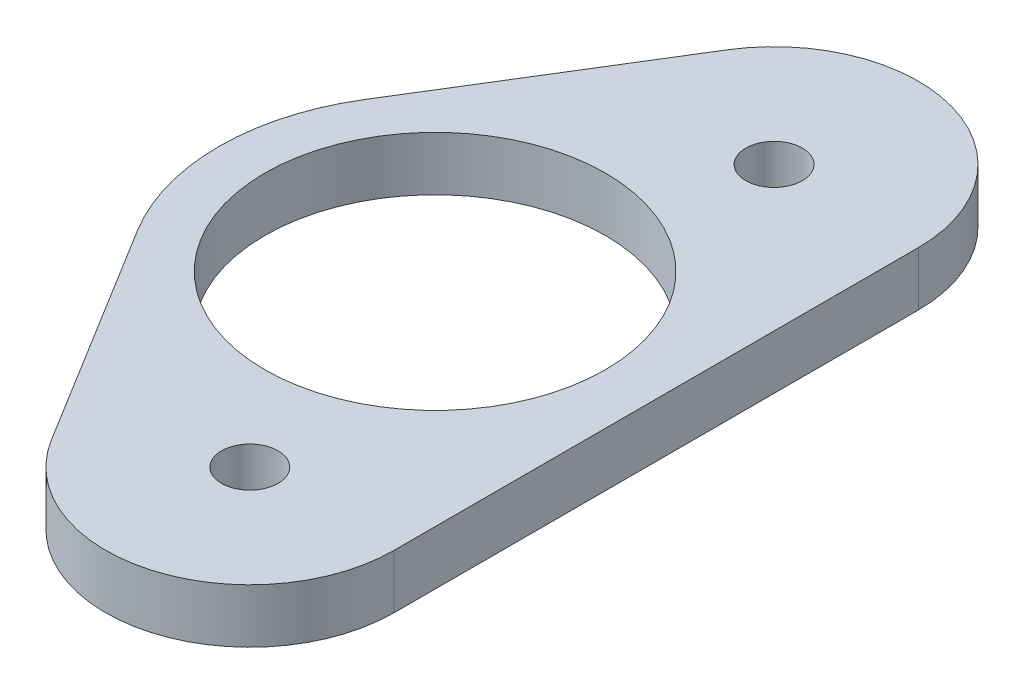
SolidWorks part; units mm, degrees
material "6061-T6 (SS)"
ref_plane "Front Plane" through (0, 0, 0) normal (0, 0, 1) x (1, 0, 0)
ref_plane "Top Plane" through (0, 0, 0) normal (0, 1, 0) x (1, 0, 0)
ref_plane "Right Plane" through (0, 0, 0) normal (1, 0, 0) x (0, 0, -1)
sketch "Sketch1" plane through (0, 0, 0) normal (0, 1, 0) x (1, 0, 0)
  line L0 (-62.5, 0) -> (0, 0) construction
  line L1 (-55.733, 23.0854) -> (0, 0) construction
  line L2 (0, 0) -> (-55.733, -23.0854) construction
  line L3 (-78.718, 9.994) -> (-66.545, 29.748)
  line L4 (-43.033, 23.0854) -> (-43.033, -23.0854)
  line L6 (-66.545, -29.748) -> (-78.718, -9.994)
  circle A0 centre (-62.5, 0) radius 15
  circle A1 centre (-55.733, 23.0854) radius 2.4892
  circle A2 centre (-55.733, -23.0854) radius 2.4892
  circle A3 centre (-55.733, 23.0854) radius 12.7
  circle A4 centre (-62.5, 0) radius 19.05
  circle A5 centre (-55.733, -23.0854) radius 12.7
  dimension "D1" = 30
  dimension "D5" = 4.9784
  dimension "D6" = 38.1
  dimension "D7" = 25.4
  dimension "D2" = 62.5
  dimension "D3" = 60.325
  dimension "D4" = 22.5
extrude "Boss-Extrude1" add sketch "Sketch1" along normal blind 4.7625 contours A5 A4 A2 | A5 A4 L6 | A4 A5 | A5 A4 A3 A0 | A3 A4 | A4 A3 A1 | A5 L4 A3 A4 | A4 A3 L3 | A5 A4 A3 A0
